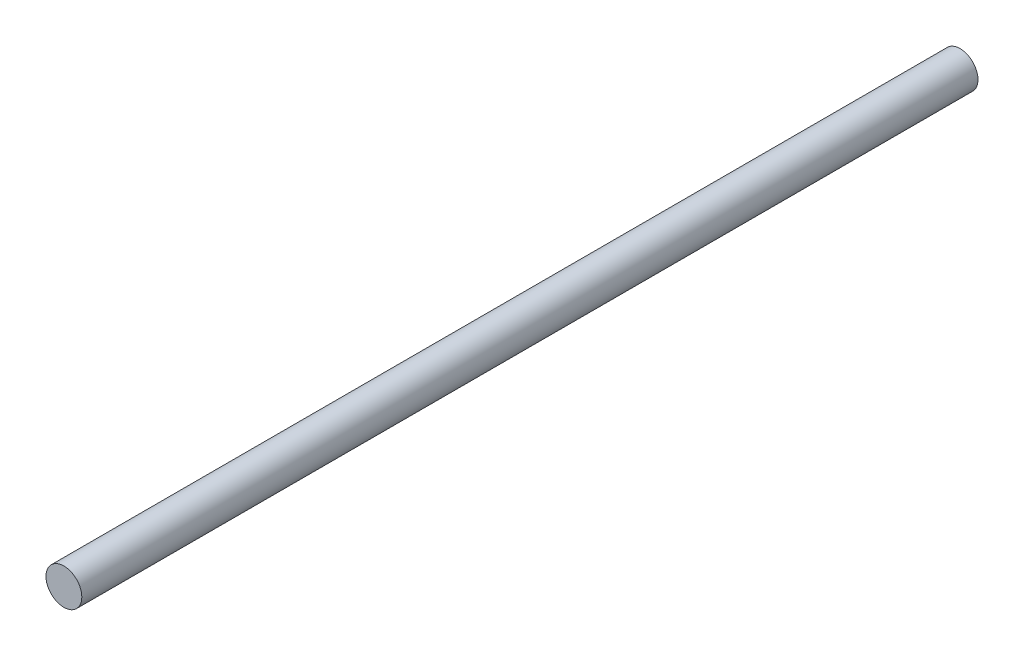
SolidWorks part; units mm, degrees
material "АД 31 ГОСТ 4784-97"
ref_plane "Plane1" through (0, 0, 0) normal (0, 0, 1) x (1, 0, 0)
ref_plane "Plane2" through (0, 0, 0) normal (0, 1, 0) x (1, 0, 0)
ref_plane "Plane3" through (0, 0, 0) normal (1, 0, 0) x (0, 0, -1)
sketch "Эскиз1" plane through (0, 0, 0) normal (0, 0, 1) x (1, 0, 0)
  circle A0 centre (0, 0) radius 4
  dimension "D1" = 8
extrude "Бобышка-Вытянуть1" add sketch "Эскиз1" along normal blind 200
